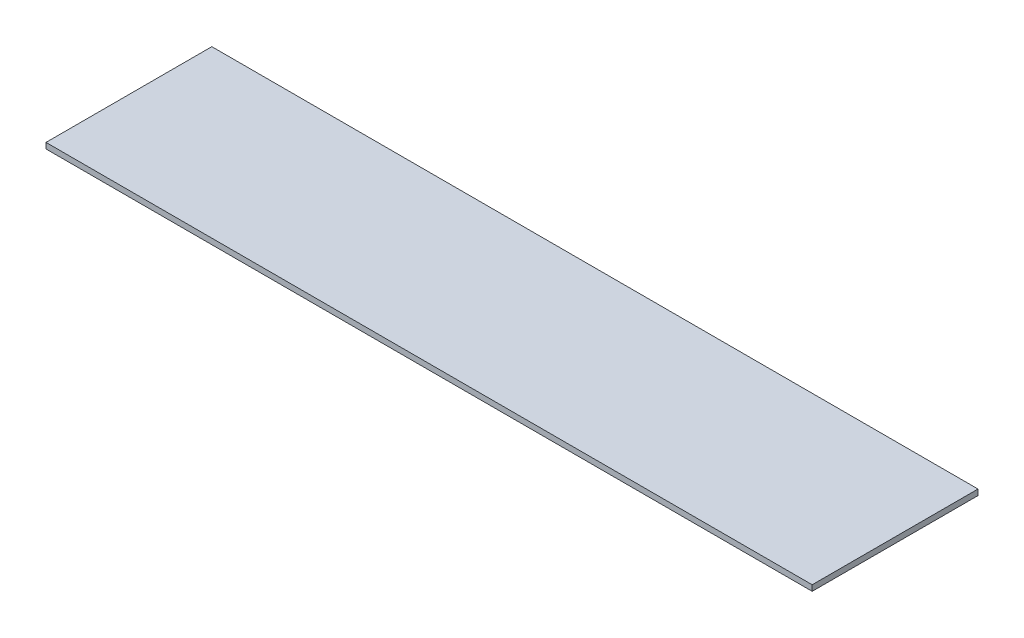
SolidWorks part; units mm, degrees
ref_plane "Płaszczyzna przednia" through (0, 0, 0) normal (0, 0, 1) x (1, 0, 0)
ref_plane "Płaszczyzna górna" through (0, 0, 0) normal (0, 1, 0) x (1, 0, 0)
ref_plane "Płaszczyzna prawa" through (0, 0, 0) normal (1, 0, 0) x (0, 0, -1)
sketch "Szkic1" plane through (0, 0, 0) normal (0, 0, 1) x (1, 0, 0)
  line L1 (-1303.8959, 6.6429) -> (36.1041, 6.6429)
  line L2 (-1303.8959, 6.6429) -> (-1303.8959, -3.3571)
  line L3 (-1303.8959, -3.3571) -> (36.1041, -3.3571)
  line L4 (36.1041, 6.6429) -> (36.1041, -3.3571)
  dimension "D1" = 10
  dimension "D2" = 1340
extrude "Dodanie-wyciągnięcie1" add sketch "Szkic1" along normal blind 290 contours L1 L4 L3 L2
